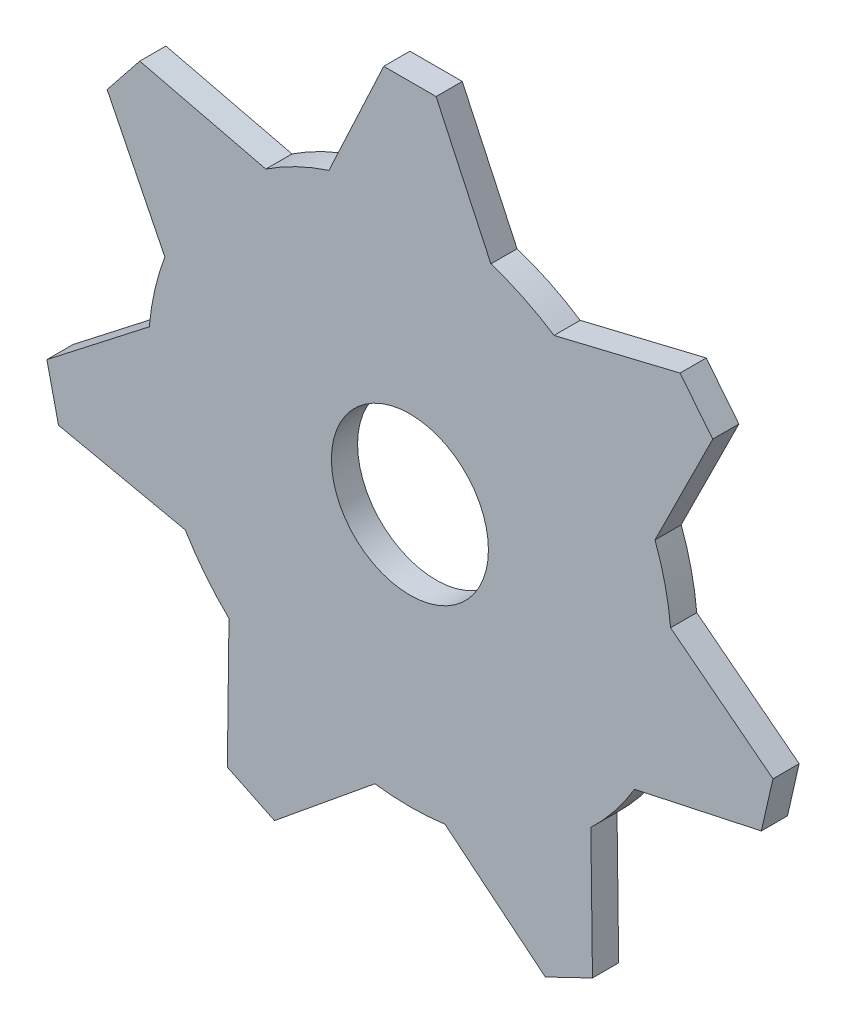
SolidWorks part; units mm, degrees
ref_plane "Front Plane" through (0, 0, 0) normal (0, 0, 1) x (1, 0, 0)
ref_plane "Top Plane" through (0, 0, 0) normal (0, 1, 0) x (1, 0, 0)
ref_plane "Right Plane" through (0, 0, 0) normal (1, 0, 0) x (0, 0, -1)
sketch "Sketch1" plane through (0, 0, 0) normal (0, 0, 1) x (1, 0, 0)
  circle A0 centre (0, 0) radius 12.7
  dimension "D1" = 25.4
extrude "Boss-Extrude1" add sketch "Sketch1" along normal blind 1.27 contours A0
sketch "Sketch3" plane through (0, 0, 1.27) normal (0, 0, 1) x (1, 0, 0)
  line L0 (0, 12.7) -> (0, 17.78) construction
  line L1 (0, 17.78) -> (-1.27, 17.78)
  line L2 (-1.27, 17.78) -> (-3.9294, 12.0768)
  line L3 (-3.9294, 12.0768) -> (3.9294, 12.0768)
  line L4 (3.9294, 12.0768) -> (1.27, 17.78)
  line L5 (1.27, 17.78) -> (0, 17.78)
  circle A0 centre (0, 0) radius 12.7 construction
  dimension "D1" = 5.08
  dimension "D2" = 1.27
  dimension "D3" = 1.27
  dimension "D4" = 65
  dimension "D5" = 65
extrude "Boss-Extrude2" add sketch "Sketch3" against normal blind 1.27
pattern_circular "CirPattern1" count 7 every 51.429 about axis through (0, 0, 0) along (0, 0, 1) of "Boss-Extrude2"
sketch "Sketch4" plane through (0, 0, 0) normal (0, 0, -1) x (-1, 0, 0)
  circle A0 centre (0, 0) radius 3.81
  dimension "D1" = 7.62
extrude "Cut-Extrude1" cut sketch "Sketch4" against normal up to surface (1.27 mm away) up to face at (0, 0, 1.27)
